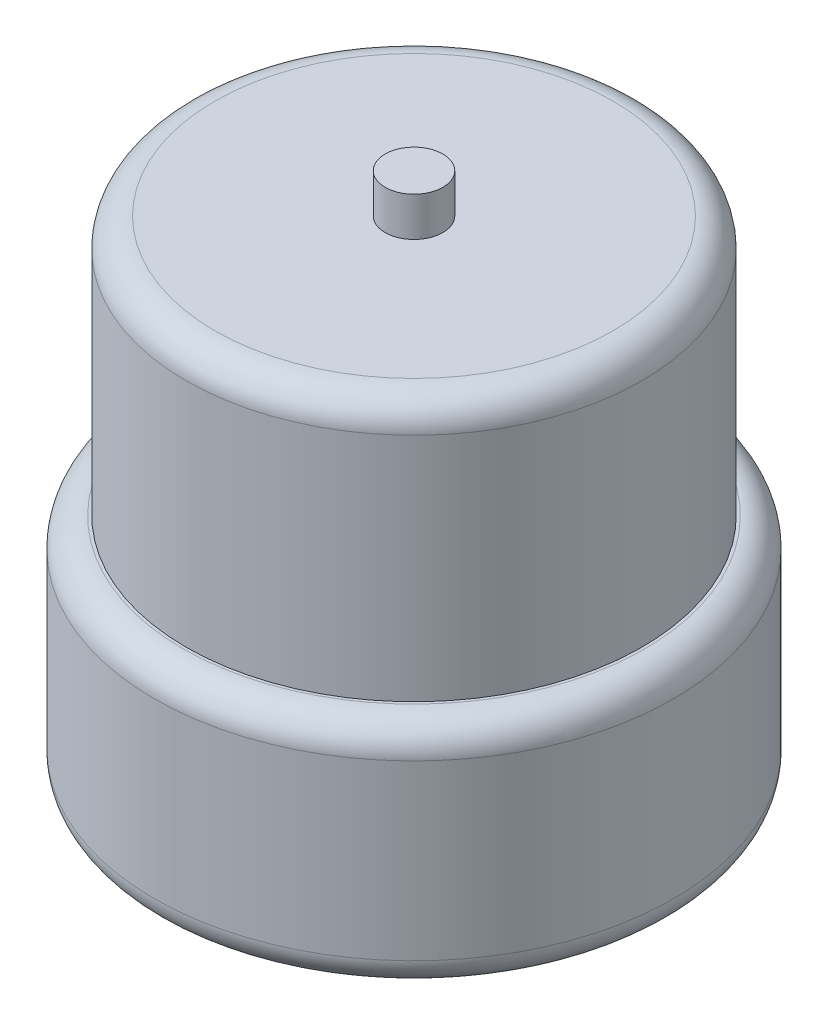
SolidWorks part; units mm, degrees
ref_plane "Front Plane" through (0, 0, 0) normal (0, 0, 1) x (1, 0, 0)
ref_plane "Top Plane" through (0, 0, 0) normal (0, 1, 0) x (1, 0, 0)
ref_plane "Right Plane" through (0, 0, 0) normal (1, 0, 0) x (0, 0, -1)
sketch "Sketch1" plane through (0, 0, 0) normal (0, 1, 0) x (1, 0, 0)
  circle A0 centre (0, 0) radius 45
  dimension "D1" = 90
extrude "Boss-Extrude1" add sketch "Sketch1" along normal blind 40
sketch "Sketch2" plane through (0, 40, 0) normal (0, 1, 0) x (1, 0, 0)
  circle A0 centre (0, 0) radius 39.5
  dimension "D1" = 79
extrude "Boss-Extrude2" add sketch "Sketch2" along normal blind 45
sketch "Sketch3" plane through (0, 85, 0) normal (0, 1, 0) x (1, 0, 0)
  circle A0 centre (0, 0) radius 5
  dimension "D1" = 10
extrude "Boss-Extrude3" add sketch "Sketch3" along normal blind 6.8
fillet "Fillet1" radius 5 3 edges at (0, 0, 45) (0, 40, 45) (0, 85, 39.5)
